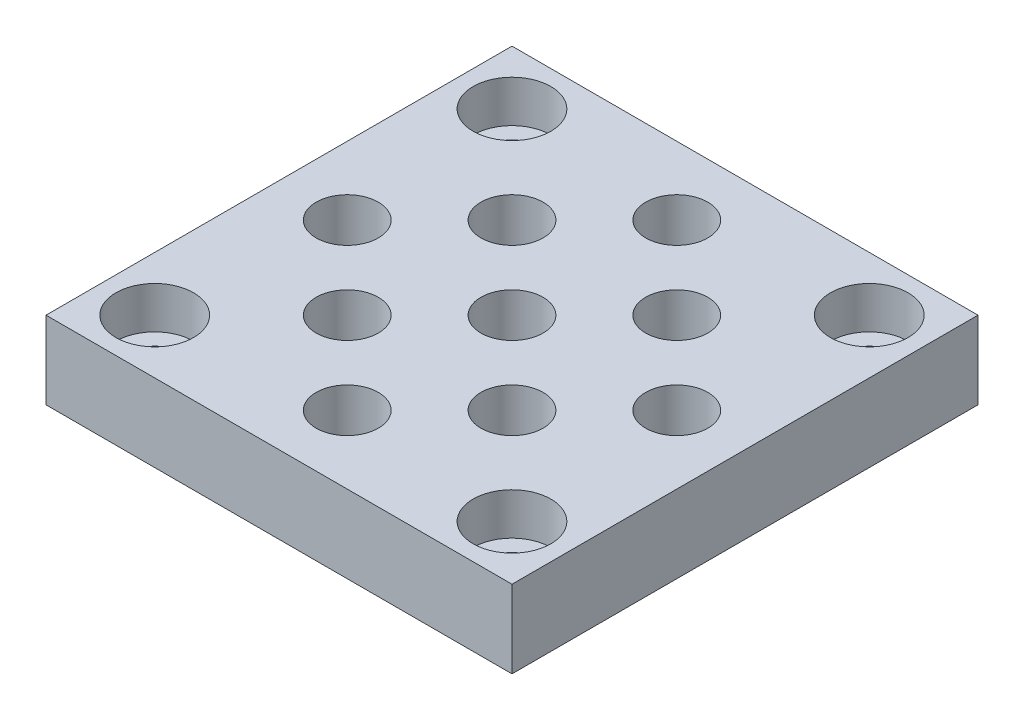
SolidWorks part; units mm, degrees
ref_plane "Alzado" through (0, 0, 0) normal (0, 0, 1) x (1, 0, 0)
ref_plane "Planta" through (0, 0, 0) normal (0, 1, 0) x (1, 0, 0)
ref_plane "Vista lateral" through (0, 0, 0) normal (1, 0, 0) x (0, 0, -1)
sketch "Croquis1" plane through (0, 0, 0) normal (0, 1, 0) x (1, 0, 0)
  line L1 (-30, 30) -> (30, 30)
  line L2 (-30, 30) -> (-30, -30)
  line L3 (-30, -30) -> (30, -30)
  line L4 (30, 30) -> (30, -30)
  line L5 (-30, 30) -> (30, -30) construction
  line L6 (-30, -30) -> (30, 30) construction
  point P0 (0, 0)
  dimension "D1" = 60
extrude "Saliente-Extruir1" add sketch "Croquis1" along normal blind 10
sketch "Croquis2" plane through (0, 10, 0) normal (0, 1, 0) x (1, 0, 0)
  line L1 (-23, 23) -> (23, 23)
  line L2 (-23, 23) -> (-23, -23)
  line L3 (-23, -23) -> (23, -23)
  line L4 (23, 23) -> (23, -23)
  line L5 (-23, 23) -> (23, -23) construction
  line L6 (-23, -23) -> (23, 23) construction
  point P0 (0, 0)
  dimension "D1" = 46
sketch "Croquis3" plane through (0, 10, 0) normal (0, 1, 0) x (1, 0, 0)
  line L0 (-23, 23) -> (23, -23) construction
  line L1 (-23, -23) -> (23, 23) construction
  circle A0 centre (0, -21.2132) radius 4
  dimension "D1" = 8
  dimension "D2" = 15
  dimension "D3" = 15
extrude "Cortar-Extruir2" cut sketch "Croquis3" against normal through all
pattern_linear "MatrizL1" count 3 spacing 15 along (0.7071, 0, -0.7071) count 3 spacing 15 along (-0.7071, 0, -0.7071) of "Cortar-Extruir2"
hole_wizard "Refrentado para tornillo con cabeza hueca de M51" positions "Croquis3D1" profile "Croquis4" counterbore size "M5" standard "ISO" end condition through all
sketch3d "Croquis3D1"
  point P0 (-23, 10, -23)
  point P3 (23, 10, -23)
  point P6 (23, 10, 23)
  point P9 (-23, 10, 23)
sketch "Croquis4" plane through (-23, 10, -23) normal (1, 0, 0) x (0, 0, 1)
  line L0 (0, 0) -> (0, 10)
  line L1 (0, 10) -> (2.75, 10)
  line L3 (2.75, 10) -> (2.75, 5.4)
  line L4 (2.75, 5.4) -> (5, 5.4)
  line L5 (5, 5.4) -> (5, 0)
  line L7 (5, 0) -> (0, 0)
  line L11 (0, -6.35) -> (0, 107.95) construction
  dimension "Diámetro de taladro hasta el siguiente" = 5.5
  dimension "Profundidad de taladro hasta el siguiente" = 10
  dimension "Diámetro de refrentado" = 10
  dimension "Profundidad de refrentado" = 5.4
hole_wizard "Taladro roscado M51" [suppressed] positions "Croquis3D2" profile "Croquis5" tap size "M5" standard "ISO"
sketch3d "Croquis3D2"
  point P0 (-23, 10, -23)
  point P3 (23, 10, -23)
  point P6 (23, 10, 23)
  point P9 (-23, 10, 23)
sketch "Croquis5" plane through (-23, 10, -23) normal (1, 0, 0) x (0, 0, 1)
  line L0 (0, 0) -> (0, 10)
  line L1 (0, 10) -> (2.1, 10)
  line L2 (2.1, 10) -> (2.1, 0)
  line L5 (2.1, 0) -> (0, 0)
  line L11 (0, -6.35) -> (0, 107.95) construction
  dimension "Diámetro de perforador para roscar hasta el siguiente" = 4.2
  dimension "Profundidad de perforador para roscar hasta el siguiente" = 10
cosmetic thread "Rosca de taladro1" [suppressed] parameters "D2"=5
cosmetic thread "Rosca de taladro2" [suppressed] parameters "D2"=5
cosmetic thread "Rosca de taladro3" [suppressed] parameters "D2"=5
cosmetic thread "Rosca de taladro4" [suppressed] parameters "D2"=5
